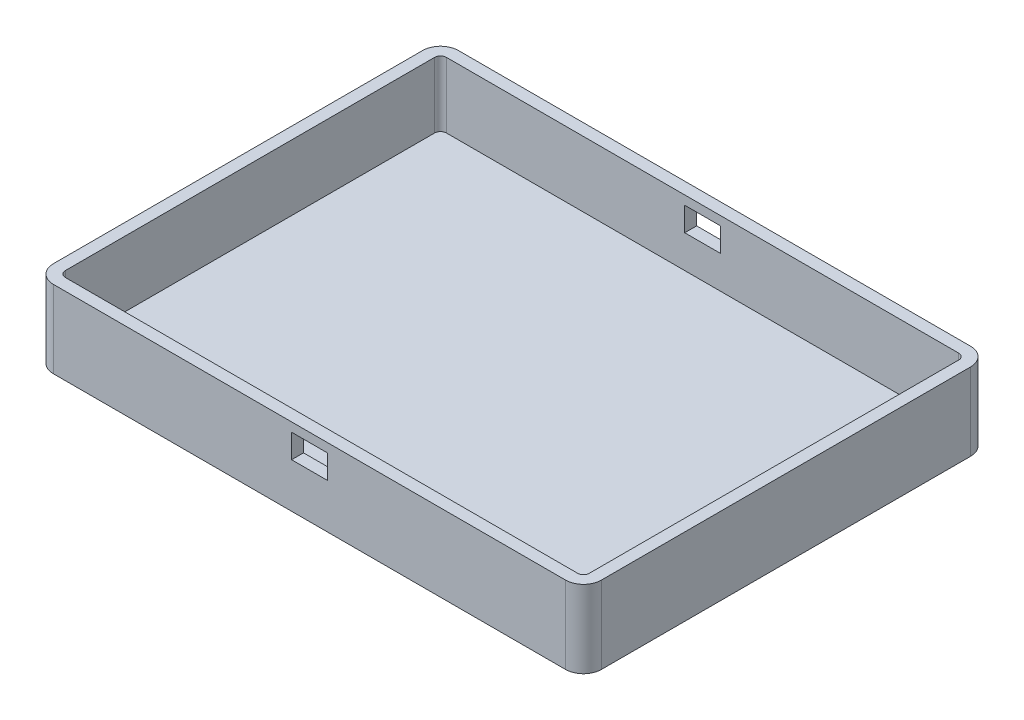
SolidWorks part; units mm, degrees
ref_plane "Front Plane" through (0, 0, 0) normal (0, 0, 1) x (1, 0, 0)
ref_plane "Top Plane" through (0, 0, 0) normal (0, 1, 0) x (1, 0, 0)
ref_plane "Right Plane" through (0, 0, 0) normal (1, 0, 0) x (0, 0, -1)
sketch "Sketch1" plane through (0, 0, 0) normal (0, 1, 0) x (1, 0, 0)
  line L1 (-46, 34) -> (46, 34)
  line L2 (-46, 34) -> (-46, -34)
  line L3 (-46, -34) -> (46, -34)
  line L4 (46, 34) -> (46, -34)
  line L5 (-46, 34) -> (46, -34) construction
  line L6 (-46, -34) -> (46, 34) construction
  point P0 (0, 0)
  dimension "D1" = 92
  dimension "D2" = 68
extrude "Boss-Extrude1" add sketch "Sketch1" along normal blind 13
fillet "Fillet1" radius 3 4 edges at (-46, 6.5, -34) (46, 6.5, -34) (46, 6.5, 34) (-46, 6.5, 34)
shell "Shell1" thickness 2
sketch "Sketch2" plane through (0, 0, 34) normal (0, 0, 1) x (1, 0, 0)
  line L0 (0, -55) -> (0, 55) construction
  line L1 (-3, 11.5) -> (3, 11.5)
  line L2 (-3, 11.5) -> (-3, 7.5)
  line L3 (-3, 7.5) -> (3, 7.5)
  line L4 (3, 11.5) -> (3, 7.5)
  line L5 (-3, 11.5) -> (3, 7.5) construction
  line L6 (-3, 7.5) -> (3, 11.5) construction
  line L7 (-43, 13) -> (43, 13) construction
  point P0 (0, 9.5)
  dimension "D1" = 1.5
  dimension "D2" = 4
  dimension "D3" = 6
extrude "Cut-Extrude1" cut sketch "Sketch2" against normal through all both and the other way through all
